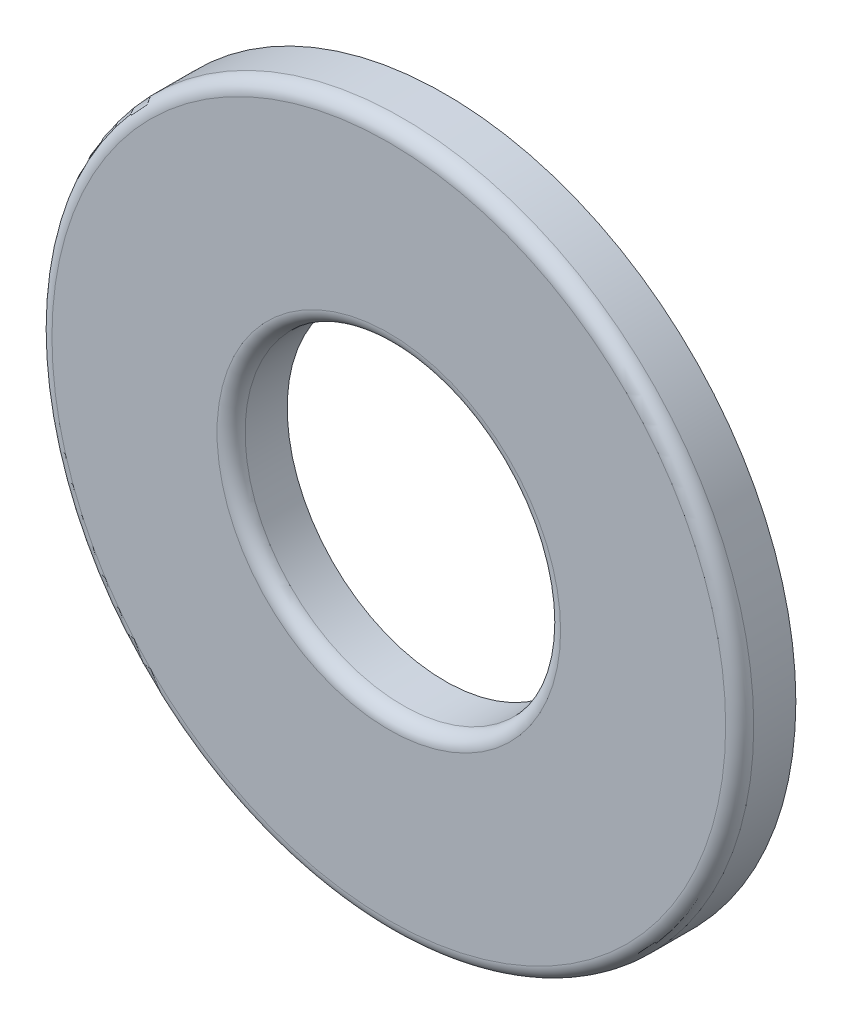
SolidWorks part; units mm, degrees
other "Imported1" parameters "D1"=0.3175, "TH"=1.0287, "Thickness"=1.27
ref_plane "Front Plane" through (0, 0, 0) normal (0, 0, 1) x (1, 0, 0)
ref_plane "Top Plane" through (0, 0, 0) normal (0, 1, 0) x (1, 0, 0)
ref_plane "Right Plane" through (0, 0, 0) normal (1, 0, 0) x (0, 0, -1)
sketch "Sketch1" plane through (0, 0, 0) normal (0, 0, 1) x (1, 0, 0)
  line L0 (-7.9375, 0) -> (7.9375, 0) construction
  line L1 (-3.5687, 0) -> (3.5687, 0) construction
  circle A0 centre (0, 0) radius 3.5687 construction
  circle A1 centre (0, 0) radius 7.9375 construction
  point P8 (0, 0)
  point P9 (0, 7.9375)
  point P11 (3.5687, 0)
  dimension "ID" = 7.1374
  dimension "OD" = 15.875
sketch "Sketch2" plane through (0, 0, 0) normal (1, 0, 0) x (0, 0, -1)
  line L0 (-0.635, 7.9375) -> (0.635, 7.9375) construction
  point P2 (0, 7.9375)
sketch "Sketch3" plane through (0, 0, 0) normal (0, 0, 1) x (1, 0, 0)
  circle A0 centre (0, 0) radius 3.5687
  circle A1 centre (0, 0) radius 7.9375
extrude "Boss-Extrude1" add sketch "Sketch3" along normal up to vertex (0.635 mm away) and the other way up to vertex (0.635 mm away) up to point (0, 7.9375, 0.635) other way up to point (0, 7.9375, -0.635)
fillet "Fillet1" radius 0.3175 2 edges at (7.9375, 0, 0.635) (3.5687, 0, 0.635)
equation "\"D1@Fillet1\"=\"Thickness@Sketch2\"/4"
